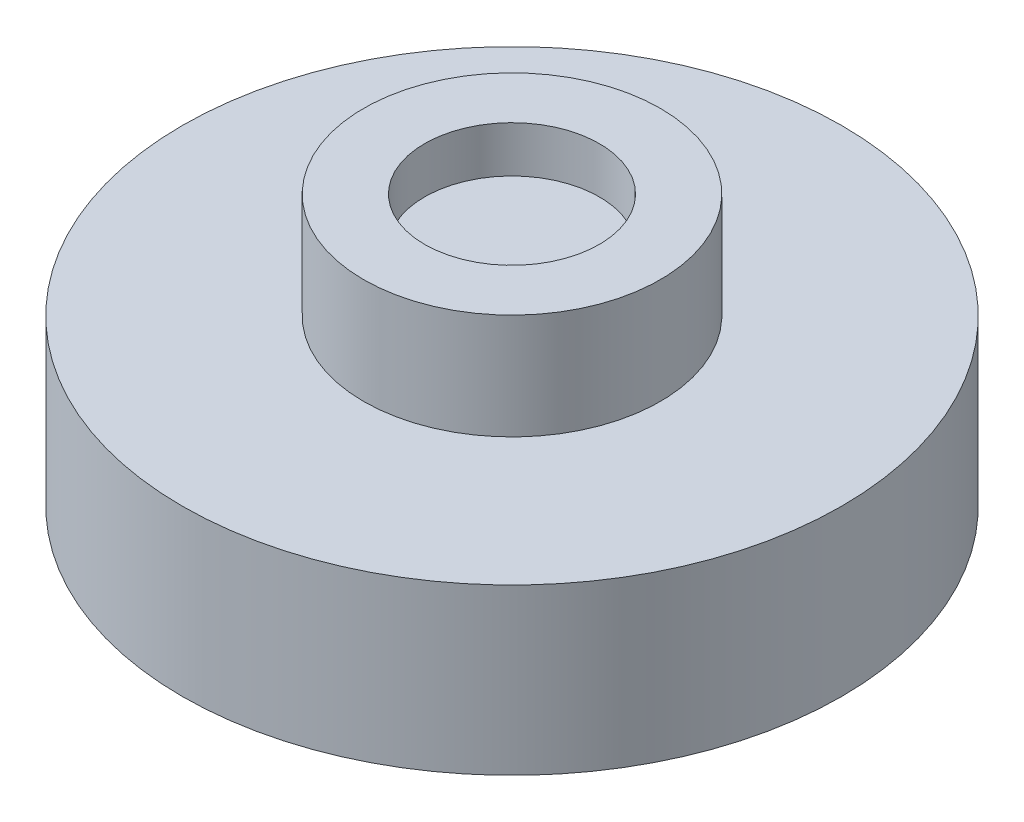
SolidWorks part; units mm, degrees
ref_plane "Front Plane" through (0, 0, 0) normal (0, 0, 1) x (1, 0, 0)
ref_plane "Top Plane" through (0, 0, 0) normal (0, 1, 0) x (1, 0, 0)
ref_plane "Right Plane" through (0, 0, 0) normal (1, 0, 0) x (0, 0, -1)
sketch "Sketch1" plane through (0, 0, 0) normal (0, 1, 0) x (1, 0, 0)
  circle A0 centre (0, 0) radius 4.5
  circle A1 centre (0, 0) radius 2.65
  dimension "D1" = 9
  dimension "D2" = 5.3
extrude "Boss-Extrude1" add sketch "Sketch1" along normal blind 3.8
sketch "Sketch2" plane through (0, 0, 0) normal (0, -1, 0) x (1, 0, 0)
  circle A0 centre (0, 0) radius 2.65
extrude "Boss-Extrude2" add sketch "Sketch2" against normal offset from surface (1.8 mm away) 2 up to face at (0, 3.8, 4.5)
sketch "Sketch3" plane through (0, 0, 0) normal (0, -1, 0) x (1, 0, 0)
  circle A0 centre (0, 0) radius 10
  dimension "D1" = 20
extrude "Boss-Extrude3" add sketch "Sketch3" along normal blind 5
sketch "Sketch4" plane through (0, 3.8, 0) normal (0, 1, 0) x (1, 0, 0)
  circle A0 centre (0, 0) radius 6.8091
extrude "Cut-Extrude1" cut sketch "Sketch4" against normal blind 0.6
